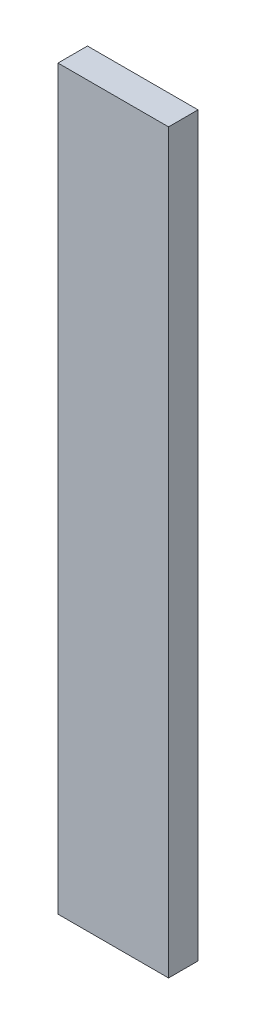
SolidWorks part; units mm, degrees
ref_plane "前视基准面" through (0, 0, 0) normal (0, 0, 1) x (1, 0, 0)
ref_plane "上视基准面" through (0, 0, 0) normal (0, 1, 0) x (1, 0, 0)
ref_plane "右视基准面" through (0, 0, 0) normal (1, 0, 0) x (0, 0, -1)
sketch "草图1" plane through (0, 0, 0) normal (0, 0, 1) x (1, 0, 0)
  line L1 (-30, 200) -> (30, 200)
  line L2 (-30, 200) -> (-30, -200)
  line L3 (-30, -200) -> (30, -200)
  line L4 (30, 200) -> (30, -200)
  line L5 (-30, 200) -> (30, -200) construction
  line L6 (-30, -200) -> (30, 200) construction
  point P0 (0, 0)
  dimension "D1" = 60
  dimension "D2" = 400
extrude "凸台-拉伸1" add sketch "草图1" along normal blind 16
